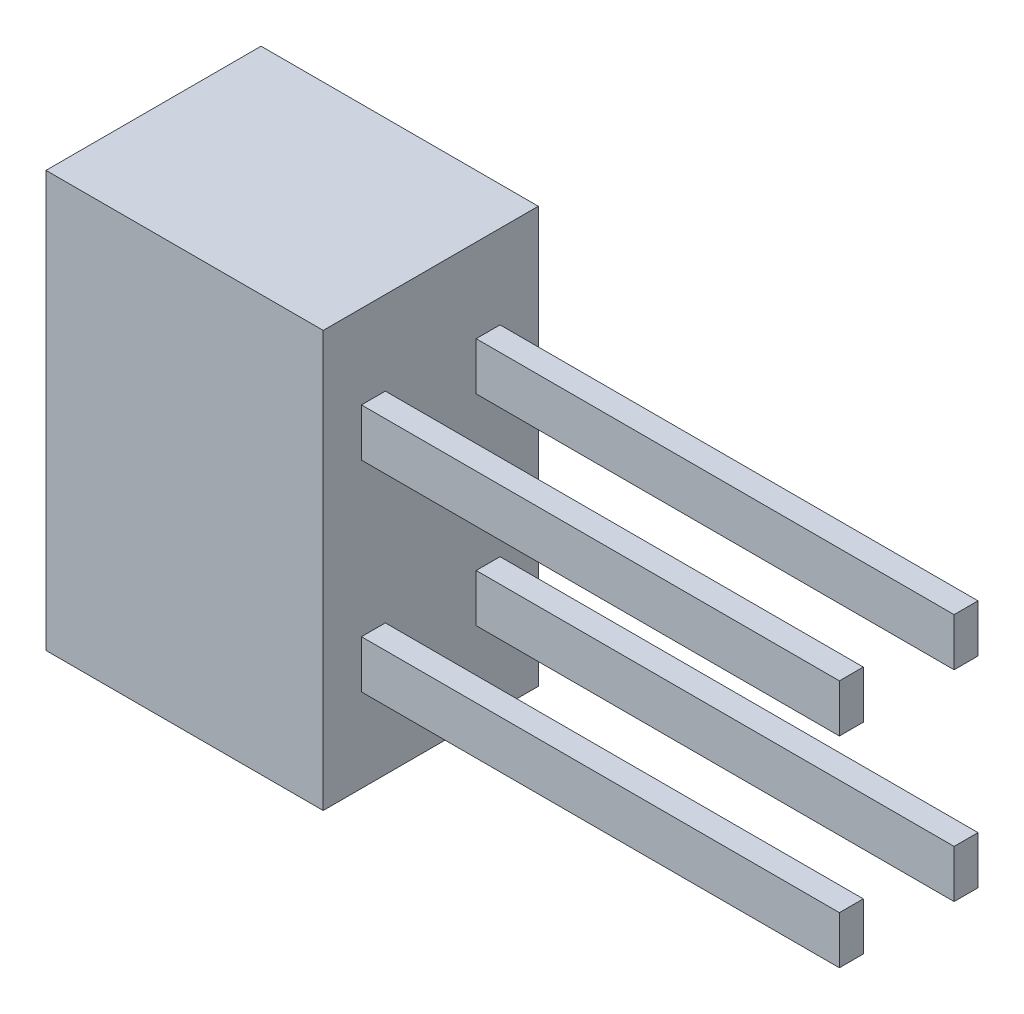
SolidWorks part; units mm, degrees
ref_plane "Front Plane" through (0, 0, 0) normal (0, 0, 1) x (1, 0, 0)
ref_plane "Top Plane" through (0, 0, 0) normal (0, 1, 0) x (1, 0, 0)
ref_plane "Right Plane" through (0, 0, 0) normal (1, 0, 0) x (0, 0, -1)
sketch "Sketch1" plane through (0, 0, 0) normal (1, 0, 0) x (0, 0, -1)
  line L1 (-2.25, -4.35) -> (2.25, -4.35)
  line L2 (-2.25, -4.35) -> (-2.25, 4.35)
  line L3 (-2.25, 4.35) -> (2.25, 4.35)
  line L4 (2.25, -4.35) -> (2.25, 4.35)
  line L5 (-2.25, -4.35) -> (2.25, 4.35) construction
  line L6 (-2.25, 4.35) -> (2.25, -4.35) construction
  point P0 (0, 0)
  dimension "D1" = 4.5
  dimension "D2" = 8.7
extrude "Boss-Extrude1" add sketch "Sketch1" along normal blind 5.8
sketch "Sketch2" plane through (5.8, 0, 0) normal (1, 0, 0) x (0, 0, -1)
  line L0 (0, -4.35) -> (0, 4.35) construction
  line L1 (-2.25, -4.35) -> (2.25, -4.35) construction
  line L2 (2.25, 4.35) -> (-2.25, 4.35) construction
  line L3 (-0.95, -4.35) -> (-0.95, 4.35) construction
  line L4 (0.95, -4.35) -> (0.95, 4.35) construction
  line L5 (-2.25, 0) -> (2.25, 0) construction
  line L6 (-0.95, -2.6) -> (-1.45, -2.6)
  line L7 (-0.95, -2.6) -> (-0.95, -1.6)
  line L8 (-0.95, -1.6) -> (-1.45, -1.6)
  line L9 (-1.45, -2.6) -> (-1.45, -1.6)
  line L10 (-2.25, 4.35) -> (-2.25, -4.35) construction
  line L11 (2.25, -4.35) -> (2.25, 4.35) construction
  line L12 (-1.45, 2.6) -> (-1.45, 1.6)
  line L13 (-0.95, 1.6) -> (-1.45, 1.6)
  line L14 (-0.95, 2.6) -> (-0.95, 1.6)
  line L15 (-0.95, 2.6) -> (-1.45, 2.6)
  line L16 (0.95, 2.6) -> (1.45, 2.6)
  line L17 (0.95, 2.6) -> (0.95, 1.6)
  line L18 (0.95, 1.6) -> (1.45, 1.6)
  line L19 (1.45, 2.6) -> (1.45, 1.6)
  line L20 (1.45, -2.6) -> (1.45, -1.6)
  line L21 (0.95, -1.6) -> (1.45, -1.6)
  line L22 (0.95, -2.6) -> (0.95, -1.6)
  line L23 (0.95, -2.6) -> (1.45, -2.6)
  line L24 (-1.45, -2.1) -> (-0.95, -2.1) construction
  line L25 (-1.45, 2.1) -> (-0.95, 2.1) construction
  line L26 (1.45, 2.1) -> (0.95, 2.1) construction
  line L27 (1.45, -2.1) -> (0.95, -2.1) construction
  point P34 (-1.2, -2.1)
  point P37 (-1.2, 2.1)
  point P42 (1.2, 2.1)
  point P43 (1.2, -2.1)
  dimension "D1" = 1.9
  dimension "D2" = 0.5
  dimension "D3" = 4.2
  dimension "D4" = 1
extrude "Boss-Extrude2" add sketch "Sketch2" along normal blind 10
sketch "Sketch3" plane through (0, 0, 2.25) normal (0, 0, 1) x (1, 0, 0)
  line L0 (0, 0) -> (5.8, 0) construction
  line L1 (0, 4.35) -> (0, -4.35) construction
  line L2 (5.8, 4.35) -> (5.8, -4.35) construction
sketch "Sketch4" plane through (5.8, 0, 0) normal (1, 0, 0) x (0, 0, -1)
  line L0 (-2.25, 0) -> (2.25, 0) construction
  line L1 (2.25, -4.35) -> (2.25, 4.35) construction
sketch "Sketch6" plane through (15.8, 0, 0) normal (1, 0, 0) x (0, 0, -1)
  line L0 (-0.95, -2.6) -> (-0.95, 2.6) construction
  point P4 (-0.95, 0)
